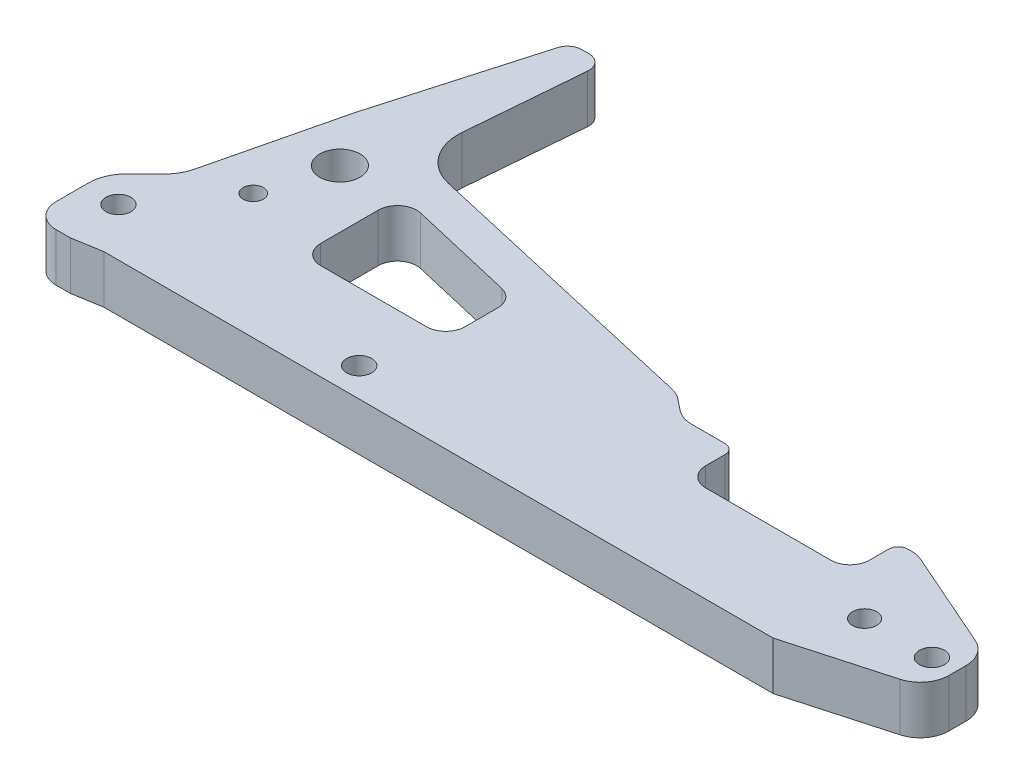
SolidWorks part; units mm, degrees
material "PE High Density"
ref_plane "Front Plane" through (0, 0, 0) normal (0, 0, 1) x (1, 0, 0)
ref_plane "Top Plane" through (0, 0, 0) normal (0, 1, 0) x (1, 0, 0)
ref_plane "Right Plane" through (0, 0, 0) normal (1, 0, 0) x (0, 0, -1)
sketch "Sketch1" plane through (0, 0, 0) normal (0, 1, 0) x (1, 0, 0)
  line L0 (164, 19) -> (139, 30)
  line L5 (164, 7) -> (139, 0)
  line L7 (-14, 14) -> (-14, 2)
  line L9 (0, 0) -> (139, 0)
  line L10 (164, 7) -> (164, 19)
  line L13 (90, 30) -> (139, 30)
  line L15 (1, 51) -> (11, 86)
  line L16 (11, 86) -> (18, 86)
  line L18 (-14, 2) -> (-14, -1)
  line L19 (-14, -1) -> (-6, -1)
  line L22 (-6, -1) -> (0, 0)
  line L23 (15, 50) -> (85, 34)
  line L24 (85, 34) -> (90, 30)
  line L25 (18, 86) -> (15, 50)
  line L26 (-14, 14) -> (-6, 22)
  line L27 (-6, 22) -> (1, 51)
  circle A0 centre (-7, 10) radius 2.6
  circle A3 centre (159, 13) radius 2.6
  circle A4 centre (5, 26) radius 2.1
  circle A6 centre (9, 40) radius 4.2
  circle A8 centre (145, 13) radius 2.5
  dimension "D9" = 5.2
  dimension "D12" = 5
  dimension "D15" = 16
  dimension "D13" = 5.2
  dimension "D17" = 4.2
  dimension "D20" = 6
  dimension "D23" = 8.4
  dimension "D27" = 13
  dimension "D3" = 46
  dimension "D4" = 7
  dimension "D5" = 25
  dimension "D6" = 25
  dimension "D7" = 166
  dimension "D8" = 12
  dimension "D10" = 7
  dimension "D11" = 8
  dimension "D14" = 40
  dimension "D16" = 5
  dimension "D18" = 7
  dimension "D19" = 12
  dimension "D21" = 10
  dimension "D22" = 75
  dimension "D24" = 16
  dimension "D25" = 15
  dimension "D26" = 14
  dimension "D28" = 12
  dimension "D29" = 10
  dimension "D30" = 3
  dimension "D31" = 8
  dimension "D32" = 70
  dimension "D33" = 16
  dimension "D34" = 14
  dimension "D35" = 8
  dimension "D36" = 8
  dimension "D37" = 29
  dimension "D38" = 4
  dimension "D39" = 30
  dimension "D40" = 13
extrude "Boss-Extrude1" add sketch "Sketch1" along normal blind 10
fillet "Fillet2" radius 6 3 edges at (164, 5, -7) (164, 5, -19) (139, 5, -30)
fillet "Fillet3" radius 3 2 edges at (11, 5, -86) (18, 5, -86)
sketch "Sketch4" plane through (0, 10, 0) normal (0, 1, 0) x (1, 0, 0)
  line L0 (21, 41) -> (21, 20)
  line L6 (21, 41) -> (51, 34)
  line L7 (51, 34) -> (51, 20)
  line L21 (51, 20) -> (21, 20)
  circle A0 centre (9, 40) radius 4.2 construction
  dimension "D1" = 12
  dimension "D2" = 1
  dimension "D3" = 21
  dimension "D5" = 30
  dimension "D8" = 14
extrude "Cut-Extrude1" cut sketch "Sketch4" against normal through all
sketch "Sketch7" plane through (0, 10, 0) normal (0, 1, 0) x (1, 0, 0)
  circle A0 centre (47, 6) radius 2.6
  circle A1 centre (9, 40) radius 4.2 construction
  dimension "D3" = 5.2
  dimension "D1" = 6
  dimension "D2" = 38
extrude "Cut-Extrude4" cut sketch "Sketch7" against normal through all
fillet "Fillet8" radius 5 1 edges at (-14, 5, 1)
fillet "Fillet9" radius 4 4 edges at (21, 5, -20) (51, 5, -34) (21, 5, -41) (51, 5, -20)
sketch "Sketch10" plane through (0, 10, 0) normal (0, 1, 0) x (1, 0, 0)
  line L0 (101, 30) -> (101, 20)
  line L1 (137.7384, 30) -> (90, 30) construction
  line L2 (101, 20) -> (135, 20)
  line L3 (135, 20) -> (135, 30)
  line L4 (135, 30) -> (101, 30)
  circle A0 centre (9, 40) radius 4.2 construction
  dimension "D3" = 92
  dimension "D1" = 10
  dimension "D2" = 0
  dimension "D4" = 34
extrude "Cut-Extrude6" cut sketch "Sketch10" against normal through all
fillet "Fillet10" radius 4 2 edges at (135, 5, -20) (101, 5, -20)
sketch "Sketch12" plane through (0, 0, 0) normal (0, 1, 0) x (1, 0, 0)
  line L4 (58, 37) -> (83, 31.0347)
  line L5 (83, 31.0347) -> (89, 26.0347)
  line L6 (89, 26.0347) -> (89, 14)
  line L7 (89, 14) -> (58, 14)
  line L8 (58, 14) -> (58, 37)
  line L9 (0, 0) -> (139, 0) construction
  circle A4 centre (-7, 10) radius 2.6 construction
  dimension "D3" = 65
  dimension "D5" = 14
  dimension "D6" = 23
  dimension "D7" = 25
  dimension "D8" = 5
  dimension "D9" = 6
extrude "Cut-Extrude7" cut sketch "Sketch12" along normal blind 6
fillet "Fillet14" radius 6 2 edges at (90, 5, -30) (85, 5, -34)
fillet "Fillet15" radius 2 2 edges at (101, 5, -30) (135, 5, -30)
fillet "Fillet16" radius 10 1 edges at (15, 5, -50)
fillet "Fillet17" radius 8 2 edges at (-6, 5, -22) (-14, 5, -14)
fillet "Fillet18" radius 4 5 edges at (83, 3, -31.0347) (89, 3, -26.0347) (89, 3, -14) (58, 3, -14) (58, 3, -37)
sketch "Sketch13" plane through (0, 0, 0) normal (0, -1, 0) x (1, 0, 0)
  line L0 (0, 0) -> (139, 0) construction
  line L1 (130.8549, -14) -> (95, -14)
  line L2 (130.8549, -14) -> (130.8549, -5)
  line L3 (130.8549, -5) -> (95, -5)
  line L4 (95, -14) -> (95, -5)
  line L5 (89, -18) -> (89, -24.1612) construction
  dimension "D1" = 5
  dimension "D2" = 9
  dimension "D3" = 6
extrude "Cut-Extrude8" cut sketch "Sketch13" against normal blind 6
fillet "Fillet19" radius 3 4 edges at (130.8549, 3, -14) (130.8549, 3, -5) (95, 3, -5) (95, 3, -14)
